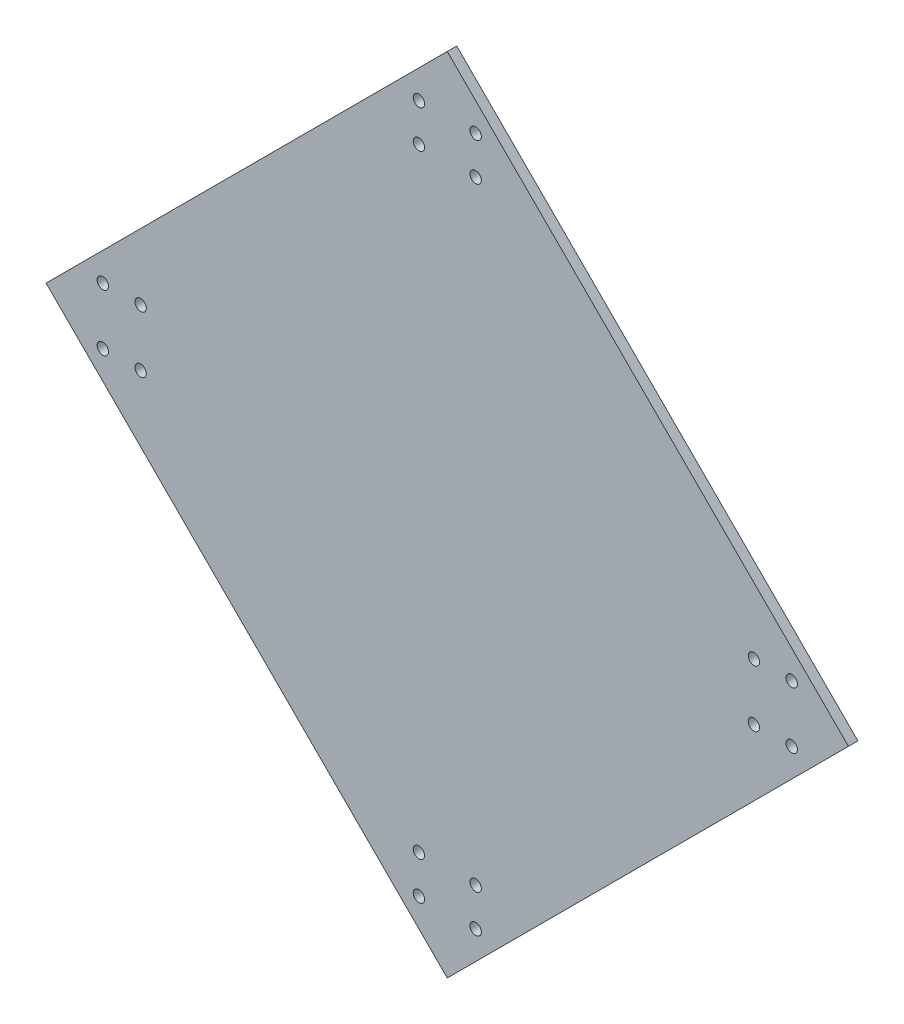
SolidWorks part; units mm, degrees
ref_plane "Front Plane" through (0, 0, 0) normal (0, 0, 1) x (1, 0, 0)
ref_plane "Top Plane" through (0, 0, 0) normal (0, 1, 0) x (1, 0, 0)
ref_plane "Right Plane" through (0, 0, 0) normal (1, 0, 0) x (0, 0, -1)
sketch "Sketch2" plane through (0, 0, 0) normal (0, 0, 1) x (1, 0, 0)
  line L0 (0, 212.132) -> (0, 0) construction
  line L1 (0, 0) -> (106.066, 106.066)
  line L2 (0, 0) -> (-106.066, 106.066)
  line L3 (-106.066, 106.066) -> (0, 212.132)
  line L4 (106.066, 106.066) -> (0, 212.132)
  line L5 (-106.066, 106.066) -> (106.066, 106.066) construction
  line L6 (-15, 197.132) -> (15, 197.132) construction
  line L7 (-25, 187.132) -> (25, 187.132) construction
  line L8 (7.5, 204.632) -> (7.5, 187.132) construction
  line L9 (-7.5, 204.632) -> (-7.5, 187.132) construction
  circle A0 centre (-7.5, 197.132) radius 1.5
  circle A1 centre (7.5, 197.132) radius 1.5
  circle A2 centre (-7.5, 187.132) radius 1.5
  circle A3 centre (7.5, 187.132) radius 1.5
  circle A4 centre (81.066, 113.566) radius 1.5
  circle A5 centre (81.066, 98.566) radius 1.5
  circle A6 centre (91.066, 98.566) radius 1.5
  circle A7 centre (91.066, 113.566) radius 1.5
  circle A8 centre (7.5, 25) radius 1.5
  circle A9 centre (-7.5, 25) radius 1.5
  circle A10 centre (-7.5, 15) radius 1.5
  circle A11 centre (7.5, 15) radius 1.5
  circle A12 centre (-81.066, 98.566) radius 1.5
  circle A13 centre (-81.066, 113.566) radius 1.5
  circle A14 centre (-91.066, 113.566) radius 1.5
  circle A15 centre (-91.066, 98.566) radius 1.5
  point P46 (0, 106.066)
  dimension "D7" = 3
  dimension "D8" = 3
  dimension "D9" = 3
  dimension "D10" = 3
  dimension "D1" = 150
  dimension "D2" = 150
  dimension "D3" = 15
  dimension "D4" = 10
  dimension "D5" = 7.5
  dimension "D6" = 7.5
  dimension "D11" = 4
extrude "Boss-Extrude1" add sketch "Sketch2" along normal blind 2.5
